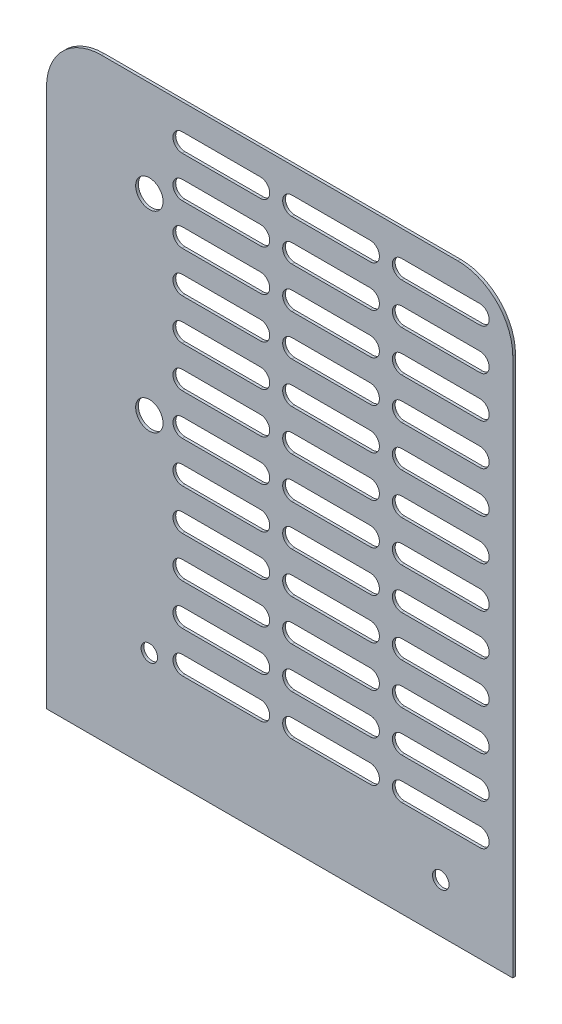
SolidWorks part; units mm, degrees
ref_plane "Plano frontal" through (0, 0, 0) normal (0, 0, 1) x (1, 0, 0)
ref_plane "Plano superior" through (0, 0, 0) normal (0, 1, 0) x (1, 0, 0)
ref_plane "Plano direito" through (0, 0, 0) normal (1, 0, 0) x (0, 0, -1)
sketch "Esboço1" plane through (0, 0, 0) normal (0, 0, 1) x (1, 0, 0)
  line L1 (55, -10) -> (185, -10)
  line L2 (35, -30) -> (35, -226.4276)
  line L3 (35, -226.4276) -> (205, -226.4276)
  line L4 (205, -30) -> (205, -226.4276)
  line L9 (84.5, -22.8655) -> (113, -22.8655) construction
  line L10 (84.5, -19.4797) -> (113, -19.4797)
  line L11 (84.5, -26.2513) -> (113, -26.2513)
  line L12 (124.5, -22.8655) -> (153, -22.8655) construction
  line L13 (124.5, -19.4797) -> (153, -19.4797)
  line L14 (124.5, -26.2513) -> (153, -26.2513)
  line L15 (164.5, -22.8655) -> (193, -22.8655) construction
  line L16 (164.5, -19.4797) -> (193, -19.4797)
  line L17 (164.5, -26.2513) -> (193, -26.2513)
  line L18 (124.5, -37.8655) -> (153, -37.8655) construction
  line L19 (124.5, -34.4797) -> (153, -34.4797)
  line L20 (124.5, -41.2513) -> (153, -41.2513)
  line L21 (164.5, -37.8655) -> (193, -37.8655) construction
  line L22 (164.5, -34.4797) -> (193, -34.4797)
  line L23 (164.5, -41.2513) -> (193, -41.2513)
  line L24 (124.5, -52.8655) -> (153, -52.8655) construction
  line L25 (124.5, -49.4797) -> (153, -49.4797)
  line L26 (124.5, -56.2513) -> (153, -56.2513)
  line L27 (164.5, -52.8655) -> (193, -52.8655) construction
  line L28 (164.5, -49.4797) -> (193, -49.4797)
  line L29 (164.5, -56.2513) -> (193, -56.2513)
  line L30 (124.5, -67.8655) -> (153, -67.8655) construction
  line L31 (124.5, -64.4797) -> (153, -64.4797)
  line L32 (124.5, -71.2513) -> (153, -71.2513)
  line L33 (164.5, -67.8655) -> (193, -67.8655) construction
  line L34 (164.5, -64.4797) -> (193, -64.4797)
  line L35 (164.5, -71.2513) -> (193, -71.2513)
  line L36 (124.5, -82.8655) -> (153, -82.8655) construction
  line L37 (124.5, -79.4797) -> (153, -79.4797)
  line L38 (124.5, -86.2513) -> (153, -86.2513)
  line L39 (164.5, -82.8655) -> (193, -82.8655) construction
  line L40 (164.5, -79.4797) -> (193, -79.4797)
  line L41 (164.5, -86.2513) -> (193, -86.2513)
  line L42 (124.5, -97.8655) -> (153, -97.8655) construction
  line L43 (124.5, -94.4797) -> (153, -94.4797)
  line L44 (124.5, -101.2513) -> (153, -101.2513)
  line L45 (164.5, -97.8655) -> (193, -97.8655) construction
  line L46 (164.5, -94.4797) -> (193, -94.4797)
  line L47 (164.5, -101.2513) -> (193, -101.2513)
  line L48 (124.5, -112.8655) -> (153, -112.8655) construction
  line L49 (124.5, -109.4797) -> (153, -109.4797)
  line L50 (124.5, -116.2513) -> (153, -116.2513)
  line L51 (164.5, -112.8655) -> (193, -112.8655) construction
  line L52 (164.5, -109.4797) -> (193, -109.4797)
  line L53 (164.5, -116.2513) -> (193, -116.2513)
  line L54 (124.5, -127.8655) -> (153, -127.8655) construction
  line L55 (124.5, -124.4797) -> (153, -124.4797)
  line L56 (124.5, -131.2513) -> (153, -131.2513)
  line L57 (164.5, -127.8655) -> (193, -127.8655) construction
  line L58 (164.5, -124.4797) -> (193, -124.4797)
  line L59 (164.5, -131.2513) -> (193, -131.2513)
  line L60 (124.5, -142.8655) -> (153, -142.8655) construction
  line L61 (124.5, -139.4797) -> (153, -139.4797)
  line L62 (124.5, -146.2513) -> (153, -146.2513)
  line L63 (164.5, -142.8655) -> (193, -142.8655) construction
  line L64 (164.5, -139.4797) -> (193, -139.4797)
  line L65 (164.5, -146.2513) -> (193, -146.2513)
  line L66 (124.5, -157.8655) -> (153, -157.8655) construction
  line L67 (124.5, -154.4797) -> (153, -154.4797)
  line L68 (124.5, -161.2513) -> (153, -161.2513)
  line L69 (164.5, -157.8655) -> (193, -157.8655) construction
  line L70 (164.5, -154.4797) -> (193, -154.4797)
  line L71 (164.5, -161.2513) -> (193, -161.2513)
  line L72 (124.5, -172.8655) -> (153, -172.8655) construction
  line L73 (124.5, -169.4797) -> (153, -169.4797)
  line L74 (124.5, -176.2513) -> (153, -176.2513)
  line L75 (164.5, -172.8655) -> (193, -172.8655) construction
  line L76 (164.5, -169.4797) -> (193, -169.4797)
  line L77 (164.5, -176.2513) -> (193, -176.2513)
  line L78 (124.5, -187.8655) -> (153, -187.8655) construction
  line L79 (124.5, -184.4797) -> (153, -184.4797)
  line L80 (124.5, -191.2513) -> (153, -191.2513)
  line L81 (164.5, -187.8655) -> (193, -187.8655) construction
  line L82 (164.5, -184.4797) -> (193, -184.4797)
  line L83 (164.5, -191.2513) -> (193, -191.2513)
  line L84 (84.5, -37.8655) -> (113, -37.8655) construction
  line L85 (84.5, -34.4797) -> (113, -34.4797)
  line L86 (84.5, -41.2513) -> (113, -41.2513)
  line L87 (84.5, -52.8655) -> (113, -52.8655) construction
  line L88 (84.5, -49.4797) -> (113, -49.4797)
  line L89 (84.5, -56.2513) -> (113, -56.2513)
  line L90 (84.5, -67.8655) -> (113, -67.8655) construction
  line L91 (84.5, -64.4797) -> (113, -64.4797)
  line L92 (84.5, -71.2513) -> (113, -71.2513)
  line L93 (84.5, -82.8655) -> (113, -82.8655) construction
  line L94 (84.5, -79.4797) -> (113, -79.4797)
  line L95 (84.5, -86.2513) -> (113, -86.2513)
  line L96 (84.5, -97.8655) -> (113, -97.8655) construction
  line L97 (84.5, -94.4797) -> (113, -94.4797)
  line L98 (84.5, -101.2513) -> (113, -101.2513)
  line L99 (84.5, -112.8655) -> (113, -112.8655) construction
  line L100 (84.5, -109.4797) -> (113, -109.4797)
  line L101 (84.5, -116.2513) -> (113, -116.2513)
  line L102 (84.5, -127.8655) -> (113, -127.8655) construction
  line L103 (84.5, -124.4797) -> (113, -124.4797)
  line L104 (84.5, -131.2513) -> (113, -131.2513)
  line L105 (84.5, -142.8655) -> (113, -142.8655) construction
  line L106 (84.5, -139.4797) -> (113, -139.4797)
  line L107 (84.5, -146.2513) -> (113, -146.2513)
  line L108 (84.5, -157.8655) -> (113, -157.8655) construction
  line L109 (84.5, -154.4797) -> (113, -154.4797)
  line L110 (84.5, -161.2513) -> (113, -161.2513)
  line L111 (84.5, -172.8655) -> (113, -172.8655) construction
  line L112 (84.5, -169.4797) -> (113, -169.4797)
  line L113 (84.5, -176.2513) -> (113, -176.2513)
  line L114 (84.5, -187.8655) -> (113, -187.8655) construction
  line L115 (84.5, -184.4797) -> (113, -184.4797)
  line L116 (84.5, -191.2513) -> (113, -191.2513)
  line L117 (84.5, -22.8655) -> (84.5, -37.8655) construction
  arc A0 (55, -10) -> (35, -30) centre (55, -30) ccw
  arc A1 (205, -30) -> (185, -10) centre (185, -30) ccw
  circle A2 centre (72.5, -45) radius 5
  circle A4 centre (72.5, -115) radius 5
  arc A5 (84.5, -19.4797) -> (84.5, -26.2513) centre (84.5, -22.8655) ccw
  arc A6 (113, -26.2513) -> (113, -19.4797) centre (113, -22.8655) ccw
  arc A7 (124.5, -19.4797) -> (124.5, -26.2513) centre (124.5, -22.8655) ccw
  arc A8 (153, -26.2513) -> (153, -19.4797) centre (153, -22.8655) ccw
  arc A9 (164.5, -19.4797) -> (164.5, -26.2513) centre (164.5, -22.8655) ccw
  arc A10 (193, -26.2513) -> (193, -19.4797) centre (193, -22.8655) ccw
  arc A11 (124.5, -34.4797) -> (124.5, -41.2513) centre (124.5, -37.8655) ccw
  arc A12 (153, -41.2513) -> (153, -34.4797) centre (153, -37.8655) ccw
  arc A13 (164.5, -34.4797) -> (164.5, -41.2513) centre (164.5, -37.8655) ccw
  arc A14 (193, -41.2513) -> (193, -34.4797) centre (193, -37.8655) ccw
  arc A15 (124.5, -49.4797) -> (124.5, -56.2513) centre (124.5, -52.8655) ccw
  arc A16 (153, -56.2513) -> (153, -49.4797) centre (153, -52.8655) ccw
  arc A17 (164.5, -49.4797) -> (164.5, -56.2513) centre (164.5, -52.8655) ccw
  arc A18 (193, -56.2513) -> (193, -49.4797) centre (193, -52.8655) ccw
  arc A19 (124.5, -64.4797) -> (124.5, -71.2513) centre (124.5, -67.8655) ccw
  arc A20 (153, -71.2513) -> (153, -64.4797) centre (153, -67.8655) ccw
  arc A21 (164.5, -64.4797) -> (164.5, -71.2513) centre (164.5, -67.8655) ccw
  arc A22 (193, -71.2513) -> (193, -64.4797) centre (193, -67.8655) ccw
  arc A23 (124.5, -79.4797) -> (124.5, -86.2513) centre (124.5, -82.8655) ccw
  arc A24 (153, -86.2513) -> (153, -79.4797) centre (153, -82.8655) ccw
  arc A25 (164.5, -79.4797) -> (164.5, -86.2513) centre (164.5, -82.8655) ccw
  arc A26 (193, -86.2513) -> (193, -79.4797) centre (193, -82.8655) ccw
  arc A27 (124.5, -94.4797) -> (124.5, -101.2513) centre (124.5, -97.8655) ccw
  arc A28 (153, -101.2513) -> (153, -94.4797) centre (153, -97.8655) ccw
  arc A29 (164.5, -94.4797) -> (164.5, -101.2513) centre (164.5, -97.8655) ccw
  arc A30 (193, -101.2513) -> (193, -94.4797) centre (193, -97.8655) ccw
  arc A31 (124.5, -109.4797) -> (124.5, -116.2513) centre (124.5, -112.8655) ccw
  arc A32 (153, -116.2513) -> (153, -109.4797) centre (153, -112.8655) ccw
  arc A33 (164.5, -109.4797) -> (164.5, -116.2513) centre (164.5, -112.8655) ccw
  arc A34 (193, -116.2513) -> (193, -109.4797) centre (193, -112.8655) ccw
  arc A35 (124.5, -124.4797) -> (124.5, -131.2513) centre (124.5, -127.8655) ccw
  arc A36 (153, -131.2513) -> (153, -124.4797) centre (153, -127.8655) ccw
  arc A37 (164.5, -124.4797) -> (164.5, -131.2513) centre (164.5, -127.8655) ccw
  arc A38 (193, -131.2513) -> (193, -124.4797) centre (193, -127.8655) ccw
  arc A39 (124.5, -139.4797) -> (124.5, -146.2513) centre (124.5, -142.8655) ccw
  arc A40 (153, -146.2513) -> (153, -139.4797) centre (153, -142.8655) ccw
  arc A41 (164.5, -139.4797) -> (164.5, -146.2513) centre (164.5, -142.8655) ccw
  arc A42 (193, -146.2513) -> (193, -139.4797) centre (193, -142.8655) ccw
  arc A43 (124.5, -154.4797) -> (124.5, -161.2513) centre (124.5, -157.8655) ccw
  arc A44 (153, -161.2513) -> (153, -154.4797) centre (153, -157.8655) ccw
  arc A45 (164.5, -154.4797) -> (164.5, -161.2513) centre (164.5, -157.8655) ccw
  arc A46 (193, -161.2513) -> (193, -154.4797) centre (193, -157.8655) ccw
  arc A47 (124.5, -169.4797) -> (124.5, -176.2513) centre (124.5, -172.8655) ccw
  arc A48 (153, -176.2513) -> (153, -169.4797) centre (153, -172.8655) ccw
  arc A49 (164.5, -169.4797) -> (164.5, -176.2513) centre (164.5, -172.8655) ccw
  arc A50 (193, -176.2513) -> (193, -169.4797) centre (193, -172.8655) ccw
  arc A51 (124.5, -184.4797) -> (124.5, -191.2513) centre (124.5, -187.8655) ccw
  arc A52 (153, -191.2513) -> (153, -184.4797) centre (153, -187.8655) ccw
  arc A53 (164.5, -184.4797) -> (164.5, -191.2513) centre (164.5, -187.8655) ccw
  arc A54 (193, -191.2513) -> (193, -184.4797) centre (193, -187.8655) ccw
  arc A55 (84.5, -34.4797) -> (84.5, -41.2513) centre (84.5, -37.8655) ccw
  arc A56 (113, -41.2513) -> (113, -34.4797) centre (113, -37.8655) ccw
  arc A57 (84.5, -49.4797) -> (84.5, -56.2513) centre (84.5, -52.8655) ccw
  arc A58 (113, -56.2513) -> (113, -49.4797) centre (113, -52.8655) ccw
  arc A59 (84.5, -64.4797) -> (84.5, -71.2513) centre (84.5, -67.8655) ccw
  arc A60 (113, -71.2513) -> (113, -64.4797) centre (113, -67.8655) ccw
  arc A61 (84.5, -79.4797) -> (84.5, -86.2513) centre (84.5, -82.8655) ccw
  arc A62 (113, -86.2513) -> (113, -79.4797) centre (113, -82.8655) ccw
  arc A63 (84.5, -94.4797) -> (84.5, -101.2513) centre (84.5, -97.8655) ccw
  arc A64 (113, -101.2513) -> (113, -94.4797) centre (113, -97.8655) ccw
  arc A65 (84.5, -109.4797) -> (84.5, -116.2513) centre (84.5, -112.8655) ccw
  arc A66 (113, -116.2513) -> (113, -109.4797) centre (113, -112.8655) ccw
  arc A67 (84.5, -124.4797) -> (84.5, -131.2513) centre (84.5, -127.8655) ccw
  arc A68 (113, -131.2513) -> (113, -124.4797) centre (113, -127.8655) ccw
  arc A69 (84.5, -139.4797) -> (84.5, -146.2513) centre (84.5, -142.8655) ccw
  arc A70 (113, -146.2513) -> (113, -139.4797) centre (113, -142.8655) ccw
  arc A71 (84.5, -154.4797) -> (84.5, -161.2513) centre (84.5, -157.8655) ccw
  arc A72 (113, -161.2513) -> (113, -154.4797) centre (113, -157.8655) ccw
  arc A73 (84.5, -169.4797) -> (84.5, -176.2513) centre (84.5, -172.8655) ccw
  arc A74 (113, -176.2513) -> (113, -169.4797) centre (113, -172.8655) ccw
  arc A75 (84.5, -184.4797) -> (84.5, -191.2513) centre (84.5, -187.8655) ccw
  arc A76 (113, -191.2513) -> (113, -184.4797) centre (113, -187.8655) ccw
  point P9 (72.5, -46.2534)
  point P12 (72.5, -112.8655)
  point P19 (98.75, -22.8655)
  point P29 (138.75, -22.8655)
  point P36 (178.75, -22.8655)
  point P43 (138.75, -37.8655)
  point P50 (178.75, -37.8655)
  point P57 (138.75, -52.8655)
  point P64 (178.75, -52.8655)
  point P71 (138.75, -67.8655)
  point P78 (178.75, -67.8655)
  point P85 (138.75, -82.8655)
  point P92 (178.75, -82.8655)
  point P99 (138.75, -97.8655)
  point P106 (178.75, -97.8655)
  point P113 (138.75, -112.8655)
  point P120 (178.75, -112.8655)
  point P127 (138.75, -127.8655)
  point P134 (178.75, -127.8655)
  point P141 (138.75, -142.8655)
  point P148 (178.75, -142.8655)
  point P155 (138.75, -157.8655)
  point P162 (178.75, -157.8655)
  point P169 (138.75, -172.8655)
  point P176 (178.75, -172.8655)
  point P183 (138.75, -187.8655)
  point P190 (178.75, -187.8655)
  point P197 (98.75, -37.8655)
  point P204 (98.75, -52.8655)
  point P211 (98.75, -67.8655)
  point P218 (98.75, -82.8655)
  point P225 (98.75, -97.8655)
  point P232 (98.75, -112.8655)
  point P239 (98.75, -127.8655)
  point P246 (98.75, -142.8655)
  point P253 (98.75, -157.8655)
  point P260 (98.75, -172.8655)
  point P267 (98.75, -187.8655)
  dimension "D1" = 3
  dimension "D3" = 15
  dimension "D2" = 12
extrude "Ressalto-extrusão1" add sketch "Esboço1" along normal blind 1
sketch "Esboço2" plane through (0, 0, 1) normal (0, 0, 1) x (1, 0, 0)
  circle A0 centre (72.5, -190) radius 3
  circle A1 centre (178.75, -208.5707) radius 3
extrude "Corte-extrusão2" cut sketch "Esboço2" against normal blind 1
